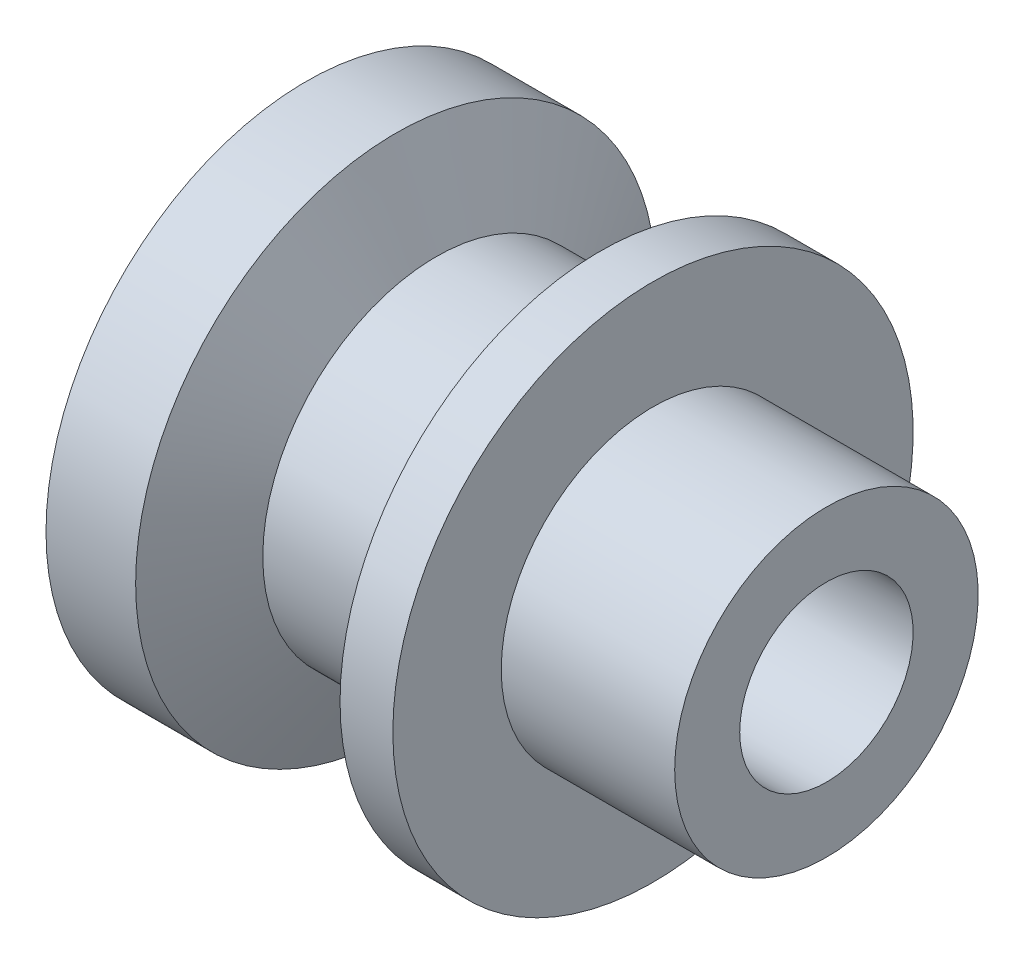
SolidWorks part; units mm, degrees
ref_plane "Front Plane" through (0, 0, 0) normal (0, 0, 1) x (1, 0, 0)
ref_plane "Top Plane" through (0, 0, 0) normal (0, 1, 0) x (1, 0, 0)
ref_plane "Right Plane" through (0, 0, 0) normal (1, 0, 0) x (0, 0, -1)
sketch "Sketch1" plane through (0, 0, 0) normal (0, 0, 1) x (1, 0, 0)
  line L0 (-49.6781, 0) -> (98.6257, 0) construction
  line L1 (-52.1521, 60) -> (-52.1521, 20)
  line L2 (-52.1521, 20) -> (67.8479, 20)
  line L3 (67.8479, 20) -> (67.8479, 35)
  line L4 (67.8479, 35) -> (27.8479, 35)
  line L5 (27.8479, 35) -> (27.8479, 60)
  line L6 (27.8479, 60) -> (15.6659, 60)
  line L7 (15.6659, 60) -> (6.3397, 40)
  line L8 (6.3397, 40) -> (-22.1521, 40)
  line L9 (-22.1521, 40) -> (-31.4783, 60)
  line L10 (-31.4783, 60) -> (-52.1521, 60)
  dimension "D1" = 40
  dimension "D2" = 40
  dimension "D3" = 120
  dimension "D4" = 25
  dimension "D5" = 50
  dimension "D6" = 30
  dimension "D7" = 15
  dimension "D8" = 20
  dimension "D9" = 25
  dimension "D10" = 40
revolve "Revolve1" add sketch "Sketch1" angle 360 about L0
